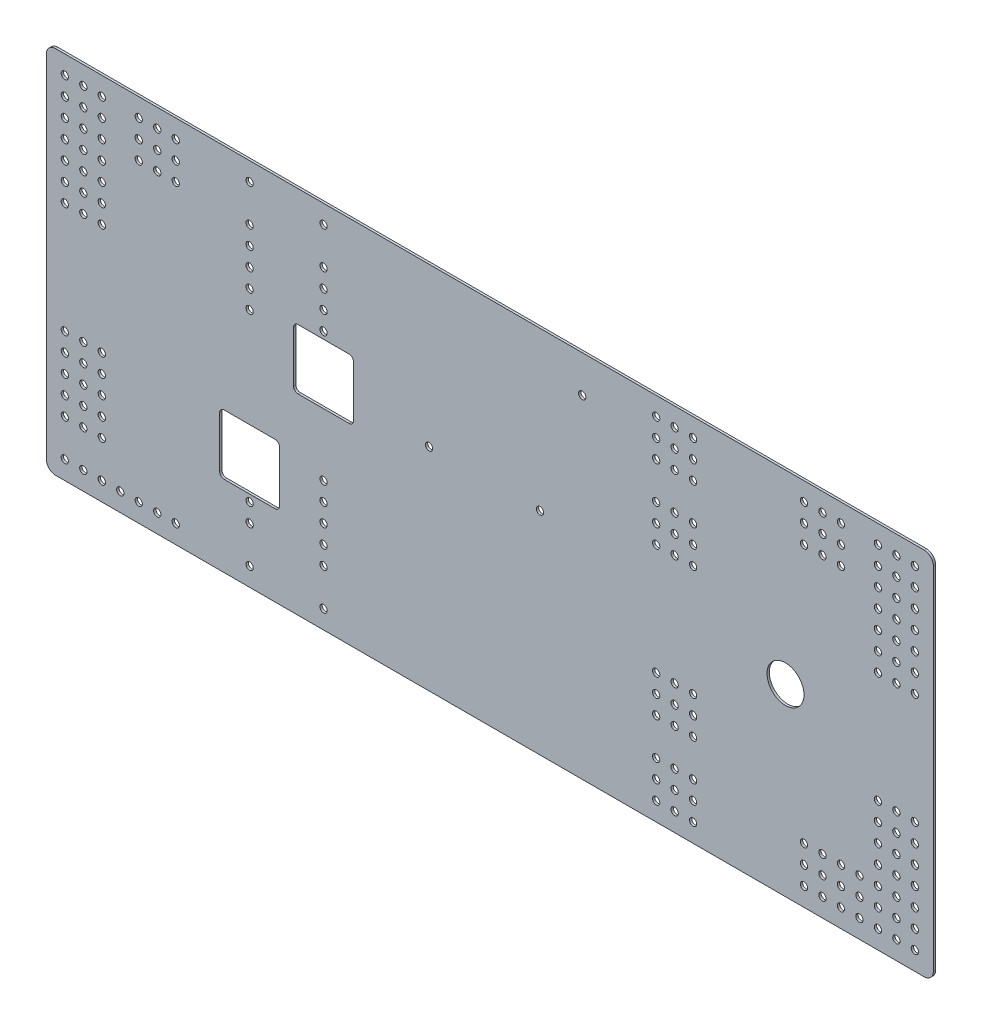
SolidWorks part; units mm, degrees
ref_plane "Front Plane" through (0, 0, 0) normal (0, 0, 1) x (1, 0, 0)
ref_plane "Top Plane" through (0, 0, 0) normal (0, 1, 0) x (1, 0, 0)
ref_plane "Right Plane" through (0, 0, 0) normal (1, 0, 0) x (0, 0, -1)
sketch "Sketch1" plane through (0, 0, 0) normal (0, 0, 1) x (1, 0, 0)
  line L0 (301.8843, 71.434) -> (301.8843, -80.966) construction
  line L1 (-148.9657, 122.234) -> (447.9343, 122.234)
  line L2 (-155.3157, 115.884) -> (-155.3157, -125.416)
  line L3 (-148.9657, -131.766) -> (447.9343, -131.766)
  line L4 (454.2843, 115.884) -> (454.2843, -125.416)
  line L6 (301.8843, -4.766) -> (404.4143, -5.6959) construction
  line L7 (352.6843, 71.434) -> (352.6843, -80.966) construction
  line L8 (301.8843, 71.434) -> (403.4843, 71.434) construction
  line L9 (301.8843, -80.966) -> (403.4843, -80.966) construction
  arc A0 (-155.3157, -125.416) -> (-148.9657, -131.766) centre (-148.9657, -125.416) ccw
  arc A1 (447.9343, -131.766) -> (454.2843, -125.416) centre (447.9343, -125.416) ccw
  arc A2 (447.9343, 122.234) -> (454.2843, 115.884) centre (447.9343, 115.884) cw
  arc A3 (-148.9657, 122.234) -> (-155.3157, 115.884) centre (-148.9657, 115.884) ccw
  circle A4 centre (352.6843, -5.2268) radius 12.7
  arc A5 (406.6593, -4.766) -> (403.4843, -7.941) centre (406.6593, -7.941) ccw construction
  point P6 (-155.3157, -131.766)
  point P11 (454.2843, 122.234)
  point P14 (-155.3157, 122.234)
  dimension "D3" = 6.35
  dimension "D4" = 25.4
  dimension "D1" = 254
  dimension "D2" = 609.6
extrude "Boss-Extrude1" add sketch "Sketch1" along normal blind 1.5875
sketch "Sketch2" plane through (0, 0, 1.5875) normal (0, 0, 1) x (1, 0, 0)
  line L0 (447.9343, 122.234) -> (-148.9657, 122.234) construction
  line L1 (-155.3157, 115.884) -> (-155.3157, -125.416) construction
  line L2 (-155.3157, -4.766) -> (454.2843, -4.766) construction
  line L3 (454.2843, -125.416) -> (454.2843, 115.884) construction
  line L4 (149.4843, 122.234) -> (149.4843, -131.766) construction
  line L5 (-148.9657, -131.766) -> (447.9343, -131.766) construction
  line L6 (454.2843, -125.416) -> (454.2843, 115.884) construction
  line L7 (447.9343, 122.234) -> (-148.9657, 122.234) construction
  line L8 (-148.9657, -131.766) -> (447.9343, -131.766) construction
  circle A0 centre (-142.6157, 109.534) radius 2.5
  circle A1 centre (-129.9157, 109.534) radius 2.5
  circle A2 centre (-117.2157, 109.534) radius 2.5
  circle A4 centre (-91.8157, 109.534) radius 2.5
  circle A5 centre (-79.1157, 109.534) radius 2.5
  circle A6 centre (-66.4157, 109.534) radius 2.5
  circle A7 centre (-129.9157, 96.834) radius 2.5
  circle A8 centre (-117.2157, 96.834) radius 2.5
  circle A10 centre (-91.8157, 96.834) radius 2.5
  circle A11 centre (-79.1157, 96.834) radius 2.5
  circle A12 centre (-66.4157, 96.834) radius 2.5
  circle A13 centre (-129.9157, 84.134) radius 2.5
  circle A14 centre (-117.2157, 84.134) radius 2.5
  circle A16 centre (-91.8157, 84.134) radius 2.5
  circle A17 centre (-79.1157, 84.134) radius 2.5
  circle A18 centre (-66.4157, 84.134) radius 2.5
  circle A19 centre (-142.6157, 96.834) radius 2.5
  circle A20 centre (-142.6157, 84.134) radius 2.5
  circle A24 centre (-142.6157, 71.434) radius 2.5
  circle A25 centre (-129.9157, 71.434) radius 2.5
  circle A26 centre (-117.2157, 71.434) radius 2.5
  circle A27 centre (-129.9157, 58.734) radius 2.5
  circle A28 centre (-117.2157, 58.734) radius 2.5
  circle A29 centre (-129.9157, 46.034) radius 2.5
  circle A30 centre (-117.2157, 46.034) radius 2.5
  circle A31 centre (-129.9157, 33.334) radius 2.5
  circle A32 centre (-117.2157, 33.334) radius 2.5
  circle A35 centre (-142.6157, 58.734) radius 2.5
  circle A36 centre (-142.6157, 46.034) radius 2.5
  circle A37 centre (-142.6157, 33.334) radius 2.5
  circle A39 centre (-142.6157, -42.866) radius 2.5
  circle A40 centre (-142.6157, -55.566) radius 2.5
  circle A41 centre (-142.6157, -68.266) radius 2.5
  circle A42 centre (-117.2157, -42.866) radius 2.5
  circle A43 centre (-129.9157, -42.866) radius 2.5
  circle A44 centre (-117.2157, -55.566) radius 2.5
  circle A45 centre (-129.9157, -55.566) radius 2.5
  circle A46 centre (-117.2157, -68.266) radius 2.5
  circle A47 centre (-129.9157, -68.266) radius 2.5
  circle A48 centre (-117.2157, -80.966) radius 2.5
  circle A49 centre (-129.9157, -80.966) radius 2.5
  circle A50 centre (-142.6157, -80.966) radius 2.5
  circle A51 centre (-142.6157, -93.666) radius 2.5
  circle A57 centre (-117.2157, -93.666) radius 2.5
  circle A58 centre (-129.9157, -93.666) radius 2.5
  circle A65 centre (-66.4157, -119.066) radius 2.5
  circle A66 centre (-79.1157, -119.066) radius 2.5
  circle A67 centre (-91.8157, -119.066) radius 2.5
  circle A68 centre (-104.5157, -119.066) radius 2.5
  circle A69 centre (-117.2157, -119.066) radius 2.5
  circle A70 centre (-129.9157, -119.066) radius 2.5
  circle A71 centre (-142.6157, -119.066) radius 2.5
  circle A72 centre (441.5843, -119.066) radius 2.5
  circle A73 centre (428.8843, -119.066) radius 2.5
  circle A74 centre (416.1843, -119.066) radius 2.5
  circle A75 centre (403.4843, -119.066) radius 2.5
  circle A76 centre (390.7843, -119.066) radius 2.5
  circle A77 centre (378.0843, -119.066) radius 2.5
  circle A78 centre (365.3843, -119.066) radius 2.5
  circle A79 centre (428.8843, -106.366) radius 2.5
  circle A80 centre (416.1843, -106.366) radius 2.5
  circle A81 centre (403.4843, -106.366) radius 2.5
  circle A82 centre (390.7843, -106.366) radius 2.5
  circle A83 centre (378.0843, -106.366) radius 2.5
  circle A84 centre (365.3843, -106.366) radius 2.5
  circle A85 centre (428.8843, -93.666) radius 2.5
  circle A86 centre (416.1843, -93.666) radius 2.5
  circle A87 centre (403.4843, -93.666) radius 2.5
  circle A88 centre (390.7843, -93.666) radius 2.5
  circle A89 centre (378.0843, -93.666) radius 2.5
  circle A90 centre (365.3843, -93.666) radius 2.5
  circle A91 centre (441.5843, -106.366) radius 2.5
  circle A92 centre (441.5843, -93.666) radius 2.5
  circle A93 centre (441.5843, -80.966) radius 2.5
  circle A94 centre (428.8843, -80.966) radius 2.5
  circle A95 centre (416.1843, -80.966) radius 2.5
  circle A96 centre (428.8843, -68.266) radius 2.5
  circle A97 centre (416.1843, -68.266) radius 2.5
  circle A98 centre (428.8843, -55.566) radius 2.5
  circle A99 centre (416.1843, -55.566) radius 2.5
  circle A100 centre (428.8843, -42.866) radius 2.5
  circle A101 centre (416.1843, -42.866) radius 2.5
  circle A102 centre (441.5843, -68.266) radius 2.5
  circle A103 centre (441.5843, -55.566) radius 2.5
  circle A104 centre (441.5843, -42.866) radius 2.5
  circle A105 centre (441.5843, 33.334) radius 2.5
  circle A106 centre (441.5843, 46.034) radius 2.5
  circle A107 centre (441.5843, 58.734) radius 2.5
  circle A108 centre (416.1843, 33.334) radius 2.5
  circle A110 centre (416.1843, 46.034) radius 2.5
  circle A112 centre (416.1843, 58.734) radius 2.5
  circle A114 centre (416.1843, 71.434) radius 2.5
  circle A116 centre (441.5843, 71.434) radius 2.5
  circle A117 centre (441.5843, 84.134) radius 2.5
  circle A118 centre (441.5843, 96.834) radius 2.5
  circle A119 centre (365.3843, 84.134) radius 2.5
  circle A120 centre (378.0843, 84.134) radius 2.5
  circle A121 centre (390.7843, 84.134) radius 2.5
  circle A123 centre (416.1843, 84.134) radius 2.5
  circle A124 centre (428.8843, 84.134) radius 2.5
  circle A125 centre (365.3843, 96.834) radius 2.5
  circle A126 centre (378.0843, 96.834) radius 2.5
  circle A127 centre (390.7843, 96.834) radius 2.5
  circle A129 centre (416.1843, 96.834) radius 2.5
  circle A130 centre (428.8843, 96.834) radius 2.5
  circle A131 centre (365.3843, 109.534) radius 2.5
  circle A132 centre (378.0843, 109.534) radius 2.5
  circle A133 centre (390.7843, 109.534) radius 2.5
  circle A135 centre (416.1843, 109.534) radius 2.5
  circle A136 centre (428.8843, 109.534) radius 2.5
  circle A137 centre (441.5843, 109.534) radius 2.5
  circle A138 centre (-15.6157, 109.534) radius 2.5
  circle A139 centre (35.1843, 109.534) radius 2.5
  circle A142 centre (-15.6157, 84.134) radius 2.5
  circle A143 centre (35.1843, 84.134) radius 2.5
  circle A144 centre (-15.6157, 71.434) radius 2.5
  circle A145 centre (35.1843, 71.434) radius 2.5
  circle A146 centre (-15.6157, 58.734) radius 2.5
  circle A147 centre (35.1843, 58.734) radius 2.5
  circle A148 centre (-15.6157, 46.034) radius 2.5
  circle A149 centre (35.1843, 46.034) radius 2.5
  circle A150 centre (-15.6157, 33.334) radius 2.5
  circle A151 centre (35.1843, 33.334) radius 2.5
  circle A152 centre (35.1843, -42.866) radius 2.5
  circle A153 centre (-15.6157, -42.866) radius 2.5
  circle A154 centre (35.1843, -55.566) radius 2.5
  circle A155 centre (-15.6157, -55.566) radius 2.5
  circle A156 centre (35.1843, -68.266) radius 2.5
  circle A157 centre (-15.6157, -68.266) radius 2.5
  circle A158 centre (35.1843, -80.966) radius 2.5
  circle A159 centre (-15.6157, -80.966) radius 2.5
  circle A160 centre (35.1843, -93.666) radius 2.5
  circle A161 centre (-15.6157, -93.666) radius 2.5
  circle A164 centre (35.1843, -119.066) radius 2.5
  circle A165 centre (-15.6157, -119.066) radius 2.5
  circle A166 centre (289.1843, 109.534) radius 2.5
  circle A167 centre (276.4843, 109.534) radius 2.5
  circle A168 centre (263.7843, 109.534) radius 2.5
  circle A169 centre (276.4843, 96.834) radius 2.5
  circle A170 centre (263.7843, 96.834) radius 2.5
  circle A171 centre (276.4843, 84.134) radius 2.5
  circle A172 centre (263.7843, 84.134) radius 2.5
  circle A175 centre (276.4843, 58.734) radius 2.5
  circle A176 centre (263.7843, 58.734) radius 2.5
  circle A177 centre (276.4843, 46.034) radius 2.5
  circle A178 centre (263.7843, 46.034) radius 2.5
  circle A179 centre (276.4843, 33.334) radius 2.5
  circle A180 centre (263.7843, 33.334) radius 2.5
  circle A181 centre (289.1843, 96.834) radius 2.5
  circle A182 centre (289.1843, 84.134) radius 2.5
  circle A184 centre (289.1843, 58.734) radius 2.5
  circle A185 centre (289.1843, 46.034) radius 2.5
  circle A186 centre (289.1843, 33.334) radius 2.5
  circle A187 centre (289.1843, -42.866) radius 2.5
  circle A188 centre (289.1843, -55.566) radius 2.5
  circle A189 centre (289.1843, -68.266) radius 2.5
  circle A192 centre (289.1843, -106.366) radius 2.5
  circle A193 centre (263.7843, -42.866) radius 2.5
  circle A194 centre (276.4843, -42.866) radius 2.5
  circle A195 centre (263.7843, -55.566) radius 2.5
  circle A196 centre (276.4843, -55.566) radius 2.5
  circle A197 centre (263.7843, -68.266) radius 2.5
  circle A198 centre (276.4843, -68.266) radius 2.5
  circle A203 centre (263.7843, -106.366) radius 2.5
  circle A204 centre (276.4843, -106.366) radius 2.5
  circle A205 centre (263.7843, -119.066) radius 2.5
  circle A206 centre (276.4843, -119.066) radius 2.5
  circle A207 centre (289.1843, -119.066) radius 2.5
  circle A208 centre (276.4843, 71.434) radius 2.5 [skipped]
  circle A209 centre (263.7843, 71.434) radius 2.5 [skipped]
  circle A210 centre (289.1843, 71.434) radius 2.5 [skipped]
  circle A211 centre (-15.6157, 96.834) radius 2.5 [skipped]
  circle A212 centre (35.1843, 96.834) radius 2.5 [skipped]
  circle A213 centre (-104.5157, 109.534) radius 2.5 [skipped]
  circle A214 centre (-104.5157, 96.834) radius 2.5 [skipped]
  circle A215 centre (-104.5157, 84.134) radius 2.5 [skipped]
  circle A216 centre (428.8843, 71.434) radius 2.5
  circle A217 centre (428.8843, 58.734) radius 2.5
  circle A218 centre (428.8843, 46.034) radius 2.5
  circle A219 centre (428.8843, 33.334) radius 2.5
  circle A220 centre (289.1843, -93.666) radius 2.5
  circle A221 centre (276.4843, -93.666) radius 2.5
  circle A222 centre (263.7843, -93.666) radius 2.5
  dimension "D3" = 5
  dimension "D7" = 5
  dimension "D11" = 5
  dimension "D14" = 5
  dimension "D19" = 5
  dimension "D25" = 5
  dimension "D27" = 38.1
  dimension "D29" = 5
  dimension "D1" = 12.7
  dimension "D2" = 12.7
  dimension "D6" = 50.8
  dimension "D8" = 12.7
  dimension "D12" = 139.7
  dimension "D13" = 12.7
  dimension "D15" = 50.8
  dimension "D16" = 12.7
  dimension "D18" = 165.1
  dimension "D20" = 12.7
  dimension "D23" = 25.4
  dimension "D24" = 50.8
  dimension "D28" = 165.1
  dimension "D4" = 7
  dimension "D5" = 3
  dimension "D9" = 3
  dimension "D10" = 4
  dimension "D17" = 7
  dimension "D21" = 3
  dimension "D22" = 7
  dimension "D26" = 4
extrude "Cut-Extrude1" cut sketch "Sketch2" against normal through all
sketch "Sketch3" plane through (0, 0, 0) normal (0, 0, -1) x (-1, 0, 0)
  line L0 (30.5382, -73.0285) -> (0.6932, -73.0285) construction
  line L1 (-1.8468, -70.4885) -> (-1.8468, -40.6435) construction
  line L2 (0.6932, -38.1035) -> (30.5382, -38.1035) construction
  line L3 (33.0782, -40.6435) -> (33.0782, -70.4885) construction
  line L4 (-20.2618, 3.1715) -> (-50.1068, 3.1715) construction
  line L5 (-52.6468, 5.7115) -> (-52.6468, 35.5565) construction
  line L6 (-50.1068, 38.0965) -> (-20.2618, 38.0965) construction
  line L7 (-17.7218, 35.5565) -> (-17.7218, 5.7115) construction
  line L8 (30.5382, -73.0285) -> (0.6932, -73.0285) construction
  line L9 (-1.8468, -70.4885) -> (-1.8468, -40.6435) construction
  line L10 (0.6932, -38.1035) -> (30.5382, -38.1035) construction
  line L11 (33.0782, -40.6435) -> (33.0782, -70.4885) construction
  line L12 (-20.2618, 3.1715) -> (-50.1068, 3.1715) construction
  line L13 (-52.6468, 5.7115) -> (-52.6468, 35.5565) construction
  line L14 (-50.1068, 38.0965) -> (-20.2618, 38.0965) construction
  line L15 (-17.7218, 35.5565) -> (-17.7218, 5.7115) construction
  line L17 (-1.8468, -34.9285) -> (33.0782, -34.9285)
  line L18 (-5.0218, -38.1035) -> (-5.0218, -73.0285)
  line L19 (-1.8468, -76.2035) -> (33.0782, -76.2035)
  line L20 (36.2532, -38.1035) -> (36.2532, -73.0285)
  line L21 (-52.6468, 41.2715) -> (-17.7218, 41.2715)
  line L22 (-55.8218, 38.0965) -> (-55.8218, 3.1715)
  line L23 (-52.6468, -0.0035) -> (-17.7218, -0.0035)
  line L24 (-14.5468, 38.0965) -> (-14.5468, 3.1715)
  arc A0 (30.5382, -73.0285) -> (33.0782, -70.4885) centre (30.5382, -70.4885) ccw construction
  arc A1 (-1.8468, -70.4885) -> (0.6932, -73.0285) centre (0.6932, -70.4885) ccw construction
  arc A2 (0.6932, -38.1035) -> (-1.8468, -40.6435) centre (0.6932, -40.6435) ccw construction
  arc A3 (33.0782, -40.6435) -> (30.5382, -38.1035) centre (30.5382, -40.6435) ccw construction
  arc A4 (-20.2618, 3.1715) -> (-17.7218, 5.7115) centre (-20.2618, 5.7115) ccw construction
  arc A5 (-52.6468, 5.7115) -> (-50.1068, 3.1715) centre (-50.1068, 5.7115) ccw construction
  arc A6 (-50.1068, 38.0965) -> (-52.6468, 35.5565) centre (-50.1068, 35.5565) ccw construction
  arc A7 (-17.7218, 35.5565) -> (-20.2618, 38.0965) centre (-20.2618, 35.5565) ccw construction
  arc A8 (30.5382, -73.0285) -> (33.0782, -70.4885) centre (30.5382, -70.4885) ccw construction
  arc A9 (-1.8468, -70.4885) -> (0.6932, -73.0285) centre (0.6932, -70.4885) ccw construction
  arc A10 (0.6932, -38.1035) -> (-1.8468, -40.6435) centre (0.6932, -40.6435) ccw construction
  arc A11 (33.0782, -40.6435) -> (30.5382, -38.1035) centre (30.5382, -40.6435) ccw construction
  arc A12 (-20.2618, 3.1715) -> (-17.7218, 5.7115) centre (-20.2618, 5.7115) ccw construction
  arc A13 (-52.6468, 5.7115) -> (-50.1068, 3.1715) centre (-50.1068, 5.7115) ccw construction
  arc A14 (-50.1068, 38.0965) -> (-52.6468, 35.5565) centre (-50.1068, 35.5565) ccw construction
  arc A15 (-17.7218, 35.5565) -> (-20.2618, 38.0965) centre (-20.2618, 35.5565) ccw construction
  arc A16 (-1.8468, -34.9285) -> (-5.0218, -38.1035) centre (-1.8468, -38.1035) ccw
  arc A17 (-5.0218, -73.0285) -> (-1.8468, -76.2035) centre (-1.8468, -73.0285) ccw
  arc A18 (33.0782, -76.2035) -> (36.2532, -73.0285) centre (33.0782, -73.0285) ccw
  arc A19 (33.0782, -34.9285) -> (36.2532, -38.1035) centre (33.0782, -38.1035) cw
  arc A20 (-55.8218, 3.1715) -> (-52.6468, -0.0035) centre (-52.6468, 3.1715) ccw
  arc A21 (-17.7218, -0.0035) -> (-14.5468, 3.1715) centre (-17.7218, 3.1715) ccw
  arc A22 (-17.7218, 41.2715) -> (-14.5468, 38.0965) centre (-17.7218, 38.0965) cw
  arc A23 (-52.6468, 41.2715) -> (-55.8218, 38.0965) centre (-52.6468, 38.0965) ccw
  dimension "D5" = 3.175
  dimension "D8" = 3.175
  dimension "D1" = 3.175
  dimension "D2" = 3.175
  dimension "D3" = 3.175
  dimension "D4" = 3.175
  dimension "D6" = 3.175
  dimension "D7" = 3.175
extrude "Cut-Extrude2" cut sketch "Sketch3" against normal through all
sketch "Sketch5" plane through (0, 0, 1.5875) normal (0, 0, 1) x (1, 0, 0)
  line L0 (447.9343, 122.234) -> (-148.9657, 122.234) construction
  circle A0 centre (212.9843, 96.834) radius 2.5
  circle A1 centre (35.1843, 109.534) radius 2.5 construction
  dimension "D2" = 177.8
  dimension "D3" = 5
  dimension "D1" = 25.4
extrude "Cut-Extrude3" cut sketch "Sketch5" against normal through all
sketch "Sketch7" plane through (0, 0, 1.5875) normal (0, 0, 1) x (1, 0, 0)
  circle A0 centre (183.8946, 13.6201) radius 2.5 construction
  circle A1 centre (107.6946, 13.6201) radius 2.5 construction
  circle A2 centre (183.8946, 13.6201) radius 2.5
  circle A3 centre (107.6946, 13.6201) radius 2.5
extrude "Cut-Extrude4" cut sketch "Sketch7" against normal through all
